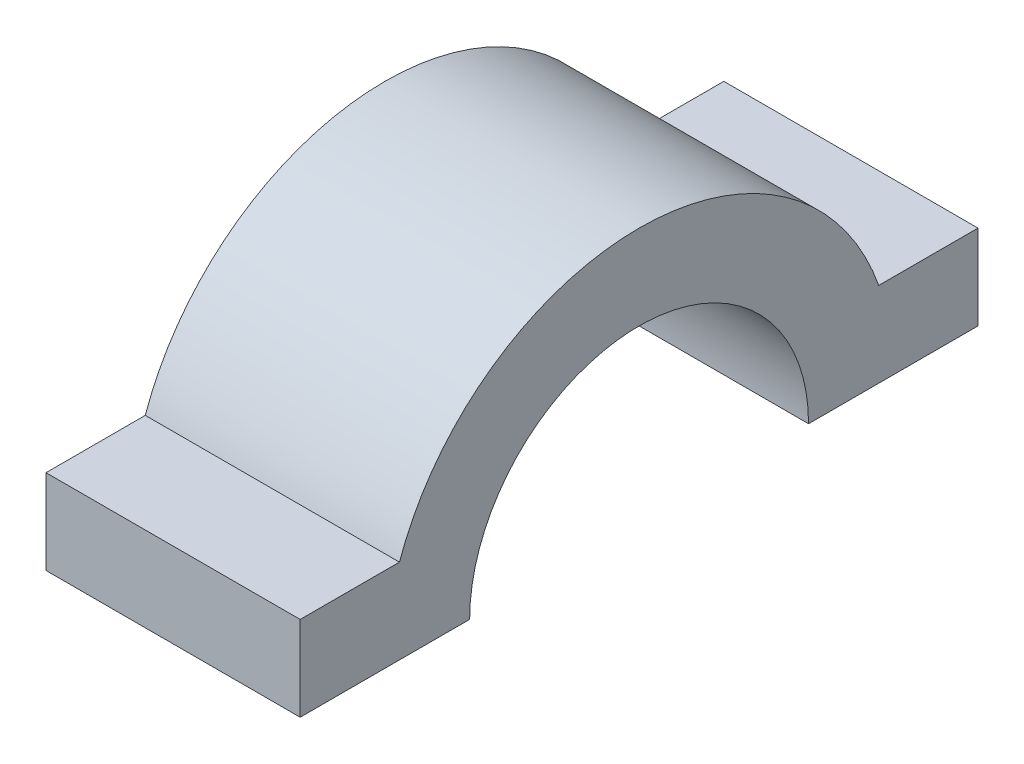
SolidWorks part; units mm, degrees
ref_plane "Alzado" through (0, 0, 0) normal (0, 0, 1) x (1, 0, 0)
ref_plane "Planta" through (0, 0, 0) normal (0, 1, 0) x (1, 0, 0)
ref_plane "Vista lateral" through (0, 0, 0) normal (1, 0, 0) x (0, 0, -1)
sketch "Croquis1" plane through (0, 0, 0) normal (1, 0, 0) x (0, 0, -1)
  line L0 (-10, 0) -> (-20, 0)
  line L1 (-20, 0) -> (-20, 5)
  line L2 (-20, 5) -> (-14.1421, 5)
  line L3 (14.1421, 5) -> (20, 5)
  line L4 (20, 5) -> (20, 0)
  line L5 (20, 0) -> (10, 0)
  arc A0 (-10, 0) -> (10, 0) centre (0, 0) cw
  arc A1 (-14.1421, 5) -> (14.1421, 5) centre (0, 0) cw
  point P10 (0.4575, 4.281)
  point P12 (0, 4.281)
  point P13 (0, 0)
  point P14 (20, -0.025)
  point P15 (0, 0)
  point P16 (-16.2745, 5)
  point P17 (0, 5)
  point P18 (-2.3529, 5)
  point P19 (0, 0)
  point P20 (-3.0719, 5)
  point P21 (0, 5)
  point P22 (0, 8.4666)
  point P23 (10, 5)
  point P24 (0, 0)
  point P25 (9.4771, 5)
  point P26 (0, -0.4902)
  dimension "D2" = 10
  dimension "D4" = 15
  dimension "D1" = 10
  dimension "D3" = 5
extrude "Saliente-Extruir1" add sketch "Croquis1" along normal blind 15
